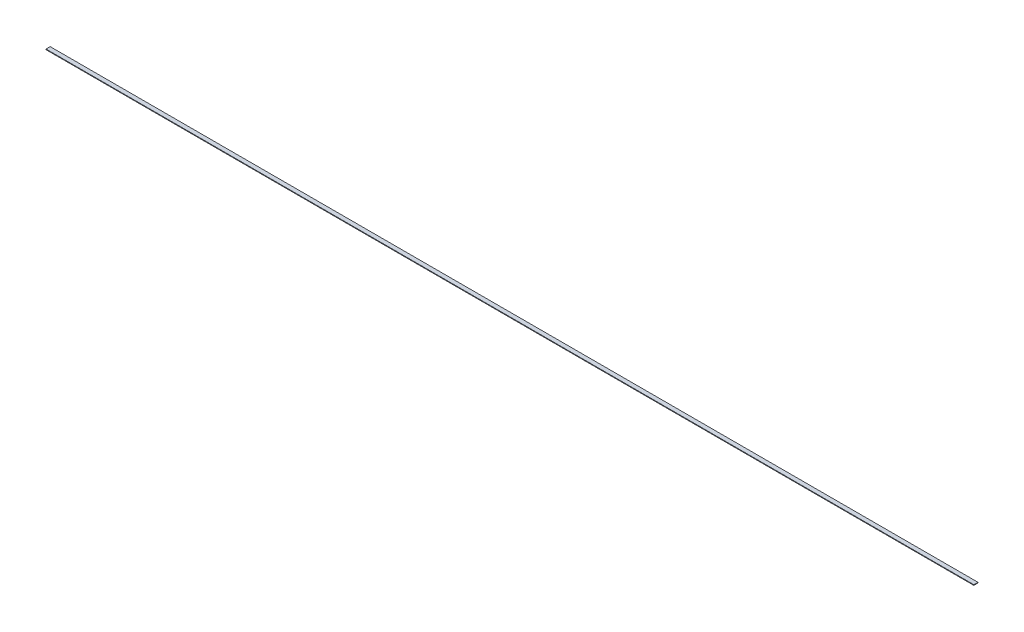
SolidWorks part; units mm, degrees
material "Rubber"
ref_plane "Front Plane" through (0, 0, 0) normal (0, 0, 1) x (1, 0, 0)
ref_plane "Top Plane" through (0, 0, 0) normal (0, 1, 0) x (1, 0, 0)
ref_plane "Right Plane" through (0, 0, 0) normal (1, 0, 0) x (0, 0, -1)
sketch "Sketch1" plane through (0, 0, 0) normal (1, 0, 0) x (0, 0, -1)
  line L1 (0, 0) -> (5.5562, 0)
  line L2 (0, 0) -> (0, 0.7937)
  line L3 (0, 0.7937) -> (5.5562, 0.7937)
  line L4 (5.5562, 0) -> (5.5562, 0.7937)
  dimension "D1" = 5.5562
  dimension "D2" = 0.7937
extrude "Boss-Extrude1" add sketch "Sketch1" along normal blind 1236.6625
